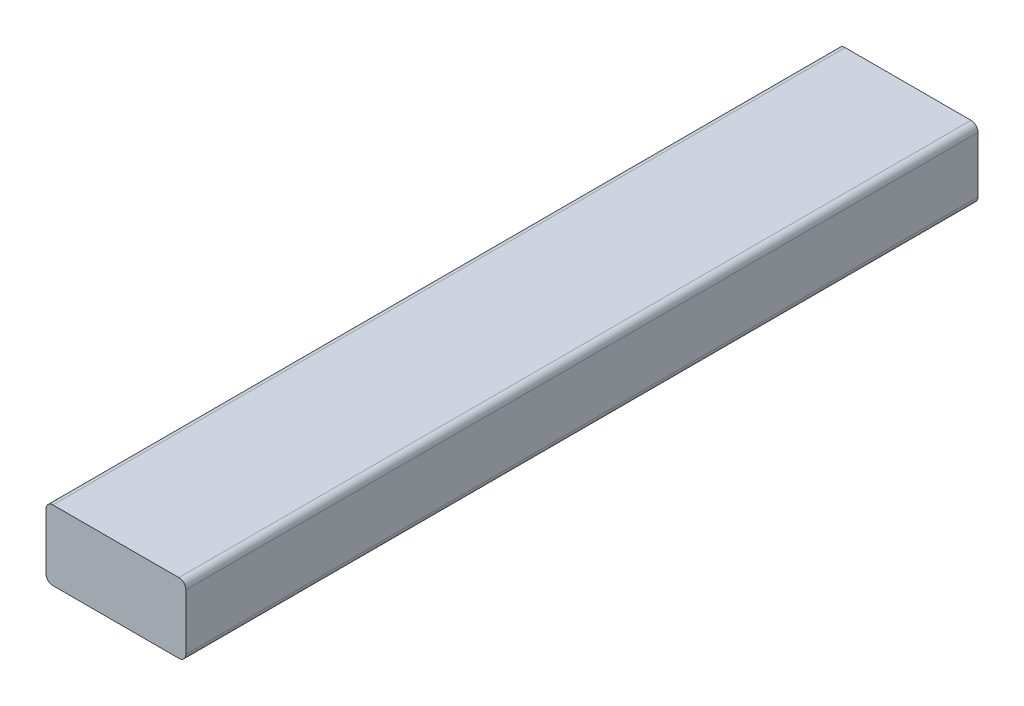
SolidWorks part; units mm, degrees
material "Balsa"
ref_plane "Front Plane" through (0, 0, 0) normal (0, 0, 1) x (1, 0, 0)
ref_plane "Top Plane" through (0, 0, 0) normal (0, 1, 0) x (1, 0, 0)
ref_plane "Right Plane" through (0, 0, 0) normal (1, 0, 0) x (0, 0, -1)
sketch "Sketch2" plane through (0, 0, 287.7) normal (0, 0, -1) x (-1, 0, 0)
  line L0 (-316.47, -12.7) -> (316.47, -12.7) construction
  line L5 (-2714.3, 38.1) -> (-2612.7, 38.1)
  line L6 (-2714.3, 38.1) -> (-2714.3, -12.7)
  line L7 (-2714.3, -12.7) -> (-2612.7, -12.7)
  line L8 (-2612.7, 38.1) -> (-2612.7, -12.7)
  line L9 (-1812.7, 38.1) -> (-2714.3, 38.1) construction
extrude "Boss-Extrude1" add sketch "Sketch2" along normal up to surface (575.4 mm away)
fillet "Fillet1" radius 5.08 4 edges at (2612.7, -12.7, 0) (2612.7, 38.1, 0) (2714.3, -12.7, 0) (2714.3, 38.1, 0)
